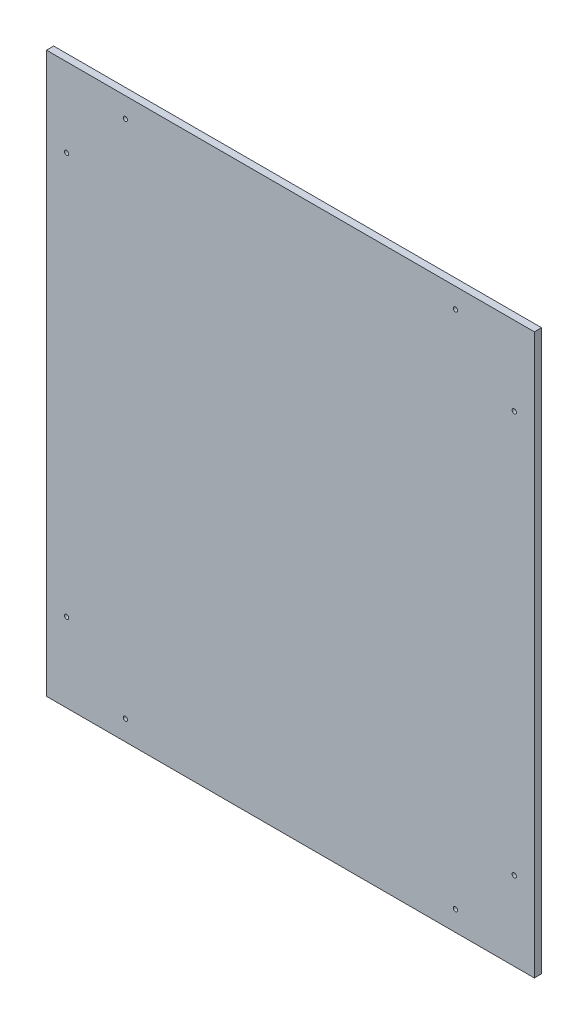
SolidWorks part; units mm, degrees
material "ABS"
ref_plane "Alzado" through (0, 0, 0) normal (0, 0, 1) x (1, 0, 0)
ref_plane "Planta" through (0, 0, 0) normal (0, 1, 0) x (1, 0, 0)
ref_plane "Vista lateral" through (0, 0, 0) normal (1, 0, 0) x (0, 0, -1)
sketch "Croquis1" plane through (0, 0, 0) normal (0, 0, 1) x (1, 0, 0)
  line L1 (-61.0528, 49.536) -> (278.9472, 49.536)
  line L2 (-61.0528, 49.536) -> (-61.0528, -340.464)
  line L3 (-61.0528, -340.464) -> (278.9472, -340.464)
  line L4 (278.9472, 49.536) -> (278.9472, -340.464)
  circle A0 centre (-47.0528, -285.464) radius 1.5
  circle A1 centre (264.9472, -285.464) radius 1.5
  circle A2 centre (264.9472, -5.464) radius 1.5
  circle A3 centre (-47.0528, -5.464) radius 1.5
  circle A4 centre (-6.0528, -326.464) radius 1.5
  circle A5 centre (223.9472, -326.464) radius 1.5
  circle A6 centre (223.9472, 35.536) radius 1.5
  circle A7 centre (-6.0528, 35.536) radius 1.5
  dimension "D3" = 55
  dimension "D11" = 14
  dimension "D13" = 14
  dimension "D1" = 340
  dimension "D2" = 390
  dimension "D4" = 14
  dimension "D5" = 14
  dimension "D6" = 55
  dimension "D7" = 14
  dimension "D8" = 55
  dimension "D9" = 55
  dimension "D10" = 14
  dimension "D12" = 55
  dimension "D14" = 55
  dimension "D15" = 14
  dimension "D16" = 55
  dimension "D17" = 14
  dimension "D18" = 55
extrude "Saliente-Extruir1" add sketch "Croquis1" along normal blind 5
